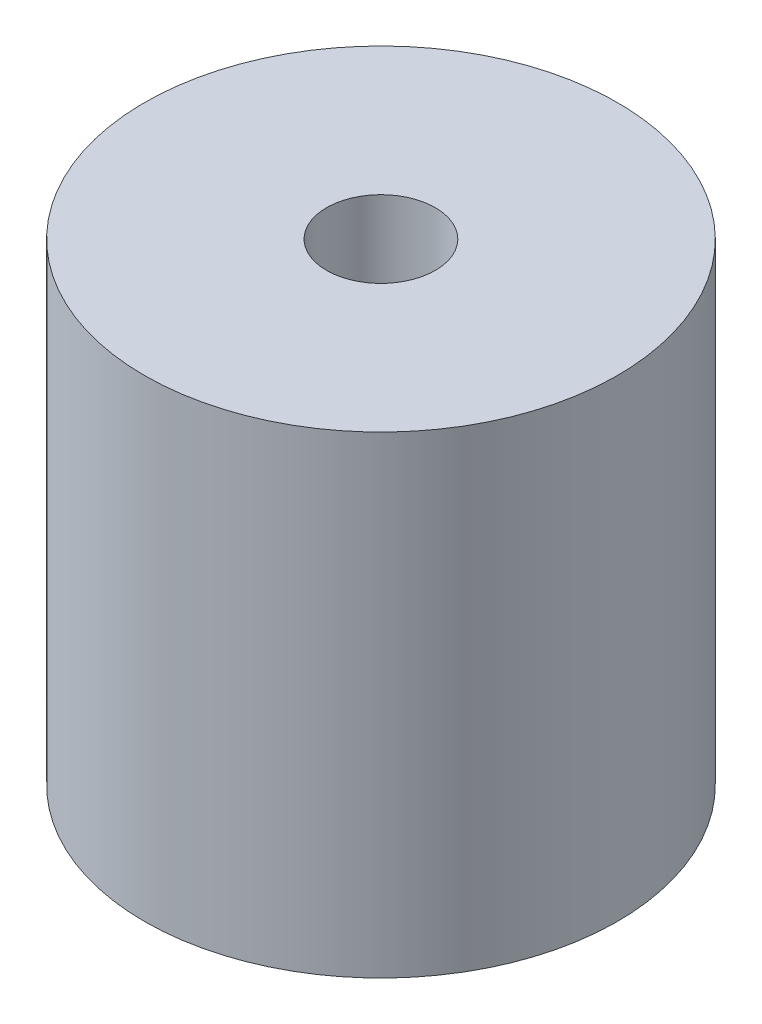
SolidWorks part; units mm, degrees
ref_plane "Спереди" through (0, 0, 0) normal (0, 0, 1) x (1, 0, 0)
ref_plane "Сверху" through (0, 0, 0) normal (0, 1, 0) x (1, 0, 0)
ref_plane "Справа" through (0, 0, 0) normal (1, 0, 0) x (0, 0, -1)
sketch "Эскиз1" plane through (0, 0, 0) normal (0, 1, 0) x (1, 0, 0)
  circle A0 centre (0, 0) radius 5
extrude "Бобышка-Вытянуть1" add sketch "Эскиз1" along normal blind 10
sketch "Эскиз2" plane through (0, 0, 0) normal (0, -1, 0) x (1, 0, 0)
  circle A0 centre (0, 0) radius 2
  circle A1 centre (0, 0) radius 4.5017
extrude "Вырез-Вытянуть1" cut sketch "Эскиз2" against normal blind 0.5
hole_wizard "Сверло под метчик  спиральное M2.21" positions "Эскиз6" profile "Эскиз5" hole size "M2.2x0.45" standard "Ansi Metric"
sketch "Эскиз6" plane through (0, 10, 0) normal (0, 1, 0) x (1, 0, 0)
  point P2 (0, 0)
sketch "Эскиз5" plane through (0, 10, 0) normal (1, 0, 0) x (0, 0, 1)
  line L0 (0, 0) -> (0, 2.691)
  line L1 (0, 2.691) -> (1.15, 2)
  line L2 (1.15, 2) -> (1.15, 0)
  line L5 (1.15, 0) -> (0, 0)
  line L10 (0, 2.691) -> (-1.15, 2) construction
  line L11 (0, -6.35) -> (0, 107.95) construction
  dimension "Диаметр отверстия" = 2.3
  dimension "Глубина отверстия" = 2
  dimension "Угол заточки сверла" = 118
